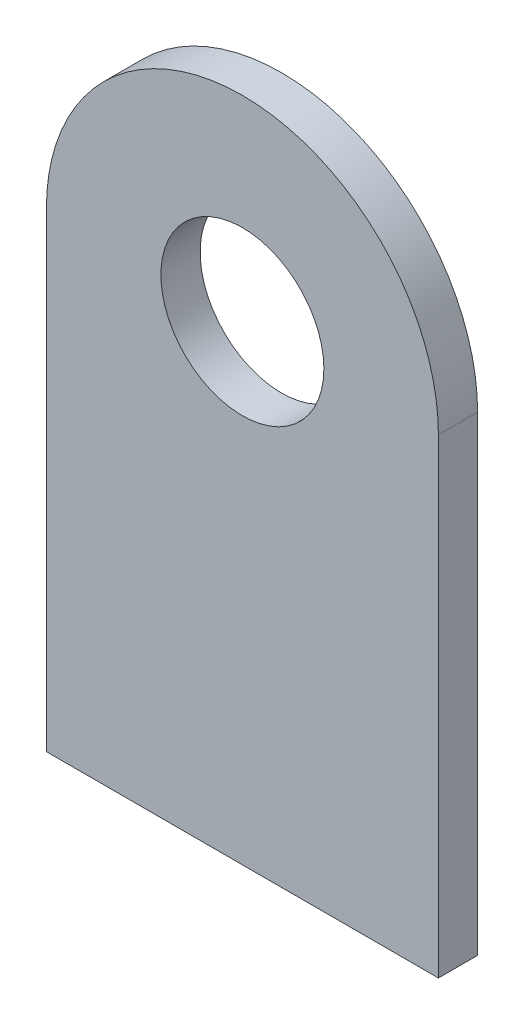
SolidWorks part; units mm, degrees
material "ASTM A36 Steel"
ref_plane "X-Y Datum" through (0, 0, 0) normal (0, 0, 1) x (1, 0, 0)
ref_plane "X-Z Datum" through (0, 0, 0) normal (0, 1, 0) x (1, 0, 0)
ref_plane "Y-Z Datum" through (0, 0, 0) normal (1, 0, 0) x (0, 0, -1)
sketch "Sketch1" plane through (0, 0, 0) normal (0, 0, 1) x (1, 0, 0)
  line L0 (-7.9375, 0) -> (-7.9375, -25.4)
  line L1 (-7.9375, -25.4) -> (7.9375, -25.4)
  line L2 (7.9375, -25.4) -> (7.9375, 0)
  circle A0 centre (0, 0) radius 7.9375
  circle A1 centre (0, 0) radius 3
  dimension "D1" = 6
  dimension "D2" = 15.875
  dimension "D3" = 25.4
extrude "Boss-Extrude1" add sketch "Sketch1" along normal blind 1.5875 contours A0 A1 | A0 L0 L1 L2 | A1
hole_wizard "M6 Clearance Hole1" positions "Sketch2" profile "Sketch3" hole size "M6" standard "ANSI Metric" end condition through all
sketch "Sketch2" plane through (0, 0, 1.5875) normal (0, 0, 1) x (1, 0, 0)
  point P0 (0, 0)
sketch "Sketch3" plane through (0, 0, 1.5875) normal (1, 0, 0) x (0, -1, 0)
  line L0 (0, 0) -> (0, 1.5875)
  line L1 (0, 1.5875) -> (3.3, 1.5875)
  line L2 (3.3, 1.5875) -> (3.3, 0)
  line L5 (3.3, 0) -> (0, 0)
  line L11 (0, -6.35) -> (0, 107.95) construction
  dimension "Thru Hole Dia." = 6.6
  dimension "Thru Hole Depth" = 1.5875
sketch "Sketch4" [suppressed] plane through (0, 0, 2.54) normal (0, 0, 1) x (1, 0, 0)
  line L1 (57.1174, 89.0913) -> (2.6108, -25.4)
  line L3 (1.0953, -29.3967) -> (-107.8628, 152.3221)
  line M3 (-7.9375, 0) -> (-7.9375, -25.4)
  line M4 (-7.9375, -25.4) -> (7.9375, -25.4)
  line M5 (7.9375, -25.4) -> (7.9375, 0)
extrude "Cut-Extrude1" [suppressed] cut sketch "Sketch4" against normal through all contours L3 M4 M3 | L1 M5 M4
sketch "Sketch5" plane through (0, 0, 1.5875) normal (0, 0, 1) x (1, 0, 0)
  line L0 (-7.9375, 0) -> (-7.9375, -25.4) construction
  line L1 (7.9375, -25.4) -> (-7.9375, -25.4)
  line L2 (7.9375, -25.4) -> (7.9375, -19.05)
  line L3 (7.9375, -19.05) -> (-7.9375, -19.05)
  line L4 (-7.9375, -25.4) -> (-7.9375, -19.05)
  dimension "D1" = 6.35
extrude "Cut-Extrude2" cut sketch "Sketch5" against normal through all
sketch "Sketch6" [suppressed] plane through (0, 0, 0) normal (0, 0, -1) x (-1, 0, 0)
  spline S0 degree 3 poles (12.0303, -22.8994) (1.6525, 0.2838) (-38.2843, -17.5937) (-27.9064, -40.7769) (-17.5286, -63.9601) (22.4081, -46.0826) (12.0303, -22.8994) (1.6525, 0.2838) (-38.2843, -17.5937) knots -0.5 0 0 0 0.5 0.5 0.5 1 1 1 1.5 1.5 1.5 weights 1 0.333333 0.333333 1 0.333333 0.333333 1 0.333333 0.333333 only from (12.0303, -22.8994) to (12.0303, -22.8994)
  spline S1 degree 3 poles (12.0303, -22.8994) (1.6525, 0.2838) (-38.2843, -17.5937) (-27.9064, -40.7769) (-17.5286, -63.9601) (22.4081, -46.0826) (12.0303, -22.8994) (1.6525, 0.2838) (-38.2843, -17.5937) knots -0.5 0 0 0 0.5 0.5 0.5 1 1 1 1.5 1.5 1.5 weights 1 0.333333 0.333333 1 0.333333 0.333333 1 0.333333 0.333333 only from (12.0303, -22.8994) to (12.0303, -22.8994)
extrude "Cut-Extrude3" [suppressed] cut sketch "Sketch6" against normal through all
